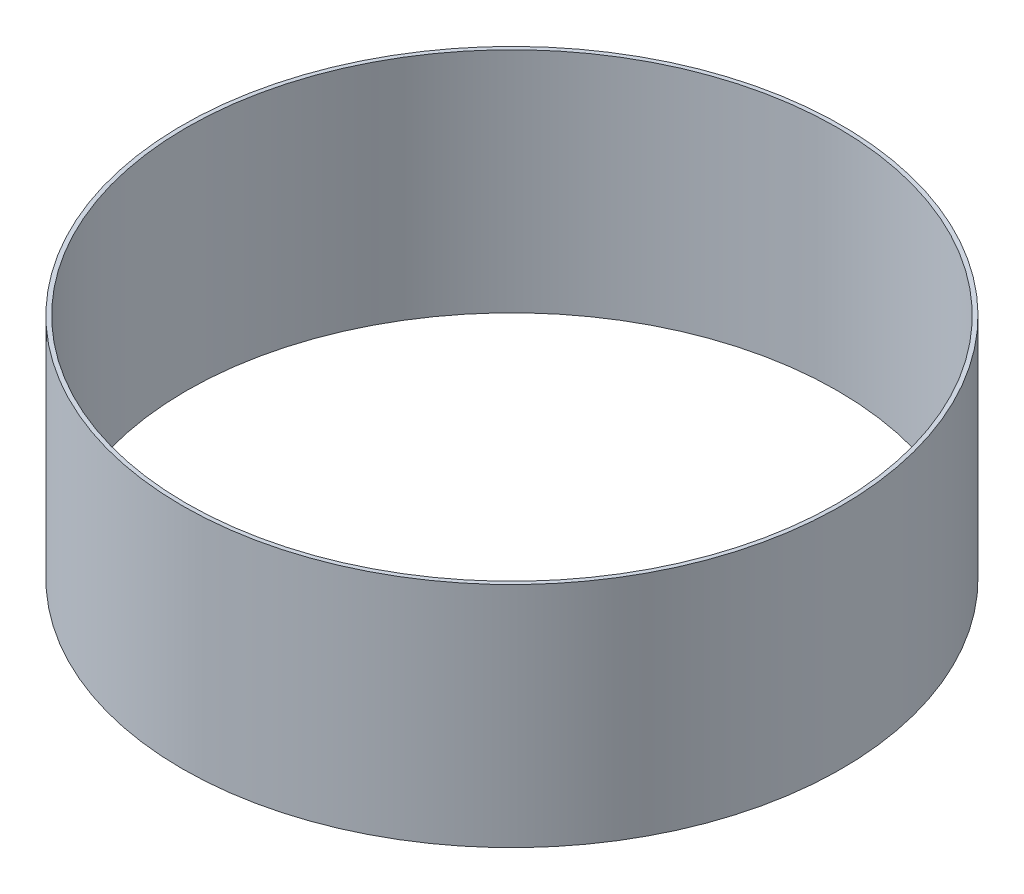
SolidWorks part; units mm, degrees
material "6061-T6 (SS)"
ref_plane "Front Plane" through (0, 0, 0) normal (0, 0, 1) x (1, 0, 0)
ref_plane "Top Plane" through (0, 0, 0) normal (0, 1, 0) x (1, 0, 0)
ref_plane "Right Plane" through (0, 0, 0) normal (1, 0, 0) x (0, 0, -1)
sketch "Sketch1" plane through (0, 0, 0) normal (0, 1, 0) x (1, 0, 0)
  circle A0 centre (0, 0) radius 127
  circle A1 centre (0, 0) radius 128.5875
  dimension "D1" = 254
  dimension "D2" = 1.5875
extrude "Boss-Extrude1" add sketch "Sketch1" along normal blind 88.9
